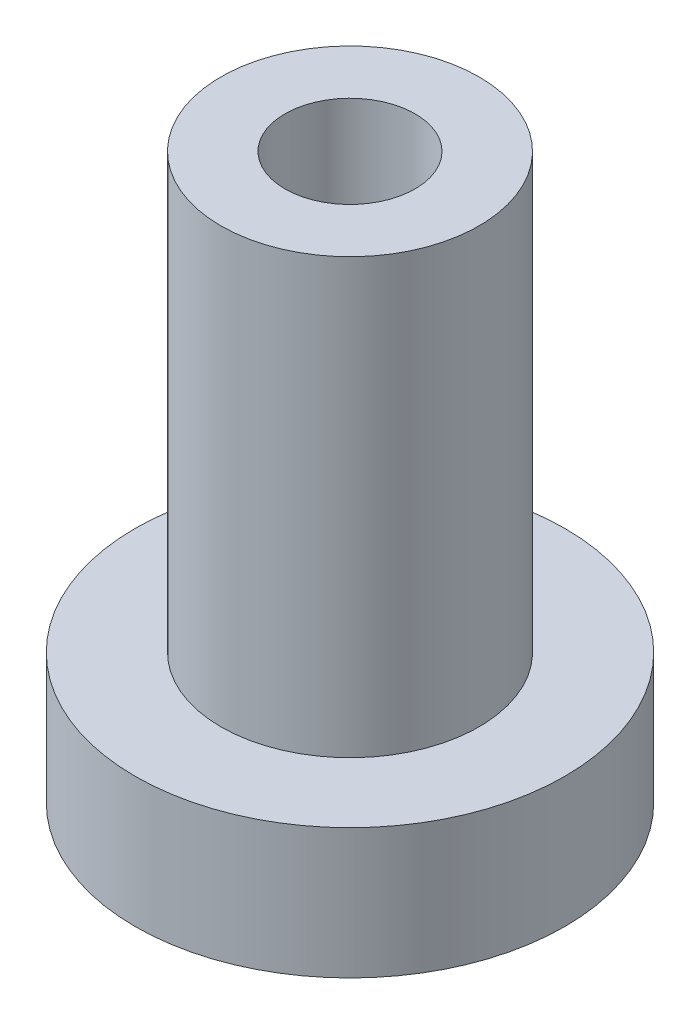
SolidWorks part; units mm, degrees
ref_plane "Спереди" through (0, 0, 0) normal (0, 0, 1) x (1, 0, 0)
ref_plane "Сверху" through (0, 0, 0) normal (0, 1, 0) x (1, 0, 0)
ref_plane "Справа" through (0, 0, 0) normal (1, 0, 0) x (0, 0, -1)
sketch "Эскиз1" plane through (0, 0, 0) normal (0, 1, 0) x (1, 0, 0)
  circle A0 centre (0, 0) radius 9.9
extrude "Бобышка-Вытянуть1" add sketch "Эскиз1" along normal blind 6
sketch "Эскиз2" plane through (0, 6, 0) normal (0, 1, 0) x (1, 0, 0)
  circle A0 centre (0, 0) radius 5.95
extrude "Бобышка-Вытянуть2" add sketch "Эскиз2" along normal blind 20
sketch "Эскиз3" plane through (0, 26, 0) normal (0, 1, 0) x (1, 0, 0)
  circle A0 centre (0, 0) radius 3
extrude "Вырез-Вытянуть1" cut sketch "Эскиз3" against normal blind 35
